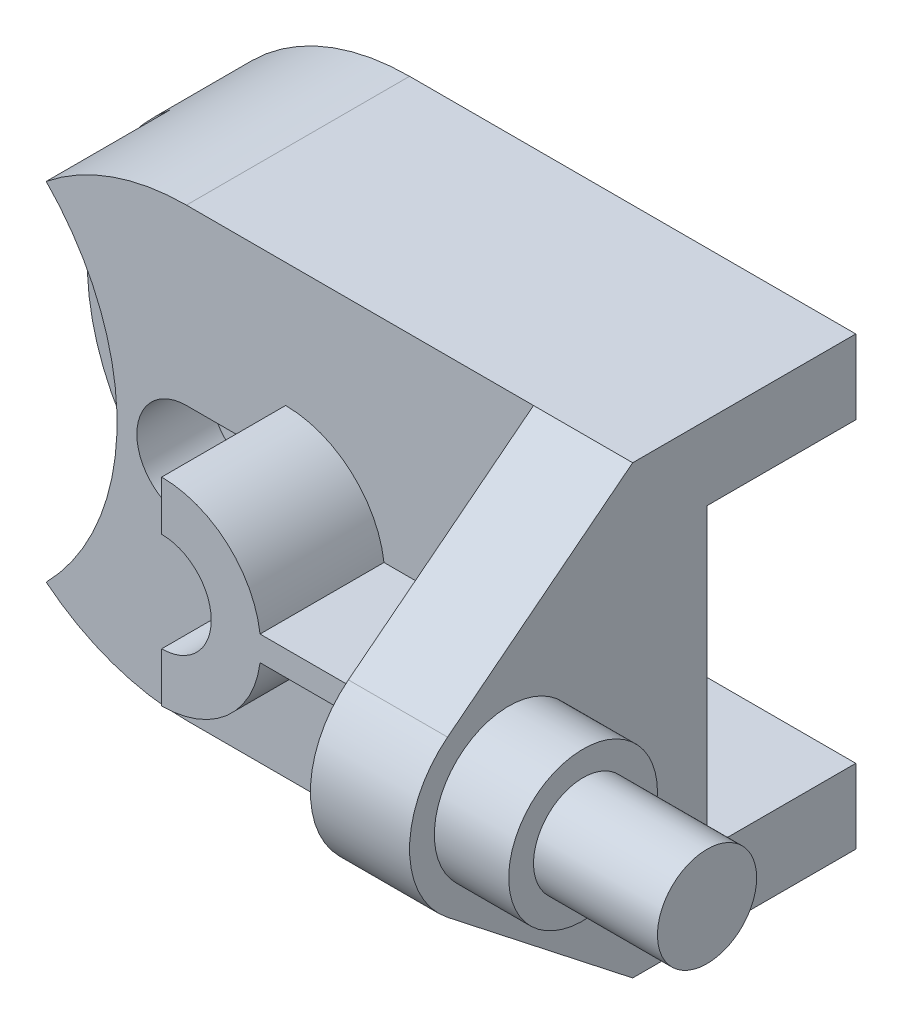
SolidWorks part; units mm, degrees
ref_plane "Front Plane" through (0, 0, 0) normal (0, 0, 1) x (1, 0, 0)
ref_plane "Top Plane" through (0, 0, 0) normal (0, 1, 0) x (1, 0, 0)
ref_plane "Right Plane" through (0, 0, 0) normal (1, 0, 0) x (0, 0, -1)
sketch "Sketch1" plane through (0, 0, 0) normal (0, 0, 1) x (1, 0, 0)
  line L1 (0, 0) -> (175, 0)
  line L2 (0, 0) -> (0, 90)
  line L3 (0, 90) -> (175, 90)
  line L4 (175, 0) -> (175, 90)
  dimension "D1" = 175
  dimension "D2" = 90
extrude "Boss-Extrude1" add sketch "Sketch1" along normal blind 90
sketch "Sketch2" plane through (0, 0, 90) normal (0, 0, 1) x (1, 0, 0)
  line L0 (175, 90) -> (0, 90) construction
  line L1 (0, 90) -> (45, 90)
  line L2 (0, 90) -> (0, 0)
  line L3 (0, 0) -> (45, 0)
  arc A0 (45, 90) -> (45, 0) centre (45, 45) ccw
  line M1 (0, 90) -> (0, 0)
  line M2 (0, 0) -> (175, 0)
  line M4 (175, 90) -> (0, 90)
  dimension "D2" = 45
  dimension "D1" = 45
  dimension "D3" = 45
  dimension "D4" = 45
extrude "Cut-Extrude1" cut sketch "Sketch2" against normal blind 90 contours A0 M4 M1 | A0 L2 M2
sketch "Sketch3" plane through (0, 0, 90) normal (0, 0, 1) x (1, 0, 0)
  line L1 (175, 90) -> (135, 90)
  line L2 (175, 90) -> (175, 60)
  line L3 (175, 60) -> (135, 60)
  line L4 (135, 90) -> (135, 60)
  line L5 (175, 0) -> (135, 0)
  line L6 (175, 0) -> (175, 30)
  line L7 (175, 30) -> (135, 30)
  line L8 (135, 0) -> (135, 30)
  dimension "D1" = 40
  dimension "D2" = 40
  dimension "D3" = 30
  dimension "D4" = 30
extrude "Cut-Extrude2" cut sketch "Sketch3" against normal blind 90
sketch "Sketch4" plane through (0, 0, 90) normal (0, 0, 1) x (1, 0, 0)
  line L1 (175, 60) -> (150, 60)
  line L2 (175, 60) -> (175, 55)
  line L3 (175, 55) -> (150, 55)
  line L4 (150, 60) -> (150, 55)
  line L5 (175, 30) -> (150, 30)
  line L6 (175, 30) -> (175, 35)
  line L7 (175, 35) -> (150, 35)
  line L8 (150, 30) -> (150, 35)
  dimension "D1" = 5
  dimension "D2" = 5
  dimension "D3" = 25
  dimension "D4" = 25
extrude "Cut-Extrude3" cut sketch "Sketch4" against normal blind 90
sketch "Sketch5" plane through (0, 0, 90) normal (0, 0, 1) x (1, 0, 0)
  arc A0 (16.7157, 80) -> (16.7157, 10) centre (-18.9914, 45) cw
  arc A1 (45, 90) -> (45, 0) centre (45, 45) ccw construction
  arc A2 (16.7157, 80) -> (16.7157, 10) centre (45, 45) ccw
  arc M10 (45, 90) -> (45, 0) centre (45, 45) ccw
  dimension "D3" = 50
  dimension "D1" = 10
  dimension "D2" = 10
extrude "Cut-Extrude4" cut sketch "Sketch5" against normal blind 70 contours A0 M10
sketch "Sketch6" plane through (0, 0, 0) normal (1, 0, 0) x (0, 0, -1)
  line L0 (-45, 90) -> (-82.3361, 60.7423)
  line L1 (0, 90) -> (-90, 90) construction
  line L2 (-82.3361, 29.2577) -> (-45, 0)
  line L4 (0, 0) -> (-90, 0) construction
  line L5 (-45, 90) -> (-90, 90)
  line L6 (-90, 90) -> (-90, 0)
  line L7 (-90, 0) -> (-45, 0)
  circle A0 centre (-70, 45) radius 20
  dimension "D1" = 40
  dimension "D2" = 45
  dimension "D3" = 70
  dimension "D4" = 45
  dimension "D5" = 45
extrude "Cut-Extrude5" cut sketch "Sketch6" along normal blind 308 contours A0 L0 L5 L6 | A0 L6 L7 L2
sketch "Sketch7" plane through (0, 0, 0) normal (0, 0, -1) x (-1, 0, 0)
  line L0 (-135, 75) -> (-45, 75)
  line L1 (-135, 90) -> (-135, 60) construction
  line L2 (-135, 75) -> (-135, 15)
  line L3 (-135, 30) -> (-135, 0) construction
  line L4 (-135, 15) -> (-45, 15)
  arc A0 (-45, 75) -> (-45, 15) centre (-45, 45) cw
  dimension "D6" = 30
  dimension "D1" = 15
  dimension "D2" = 15
  dimension "D3" = 90
  dimension "D4" = 90
  dimension "D5" = 60
  dimension "D8" = 30
extrude "Cut-Extrude6" cut sketch "Sketch7" against normal blind 30
sketch "Sketch8" plane through (175, 0, 0) normal (1, 0, 0) x (0, 0, -1)
  line L0 (-87.3205, 55) -> (0, 55)
  line L1 (0, 55) -> (0, 35)
  line L2 (0, 35) -> (-87.3205, 35)
  circle A0 centre (-70, 45) radius 10
  arc A1 (-87.3205, 55) -> (-87.3205, 35) centre (-70, 45) ccw construction
  arc A2 (-87.3205, 55) -> (-87.3205, 35) centre (-70, 45) ccw
  point P2 (-90, 45)
  arc M1 (-87.3205, 55) -> (-87.3205, 35) centre (-70, 45) ccw
  line M2 (-87.3205, 35) -> (0, 35)
  line M3 (0, 35) -> (0, 55)
  line M4 (0, 55) -> (-87.3205, 55)
  dimension "D1" = 20
  dimension "D2" = 20
  dimension "D3" = 45
extrude "Cut-Extrude7" cut sketch "Sketch8" against normal blind 25 contours A0 L0 M1 M2 | A0 L2 M3 M4
sketch "Sketch9" plane through (150, 0, 0) normal (1, 0, 0) x (0, 0, -1)
  line L0 (-83.2288, 60) -> (0, 60)
  line L1 (0, 60) -> (0, 30)
  line L2 (0, 30) -> (-83.2288, 30)
  circle A0 centre (-70, 45) radius 15
  arc A1 (-83.2288, 60) -> (-83.2288, 30) centre (-70, 45) ccw
  line M2 (0, 60) -> (-83.2288, 60)
  arc M3 (-83.2288, 60) -> (-83.2288, 30) centre (-70, 45) ccw
  line M4 (-83.2288, 30) -> (0, 30)
  line M5 (0, 30) -> (0, 60)
  dimension "D1" = 30
extrude "Cut-Extrude8" cut sketch "Sketch9" against normal blind 15 contours A0 L0 M3 M4 | A0 L2 M5 M2
ref_plane "Plane1" through (115, 0, 0) normal (1, 0, 0) x (0, 0, -1)
sketch "Sketch10" plane through (115, 0, 0) normal (1, 0, 0) x (0, 0, -1)
  line L1 (-45, 90) -> (-90, 90)
  line L2 (-45, 90) -> (-45, 0)
  line L3 (-45, 0) -> (-90, 0)
  line L4 (-90, 90) -> (-90, 0)
  dimension "D1" = 45
  dimension "D2" = 45
  dimension "D3" = 0
  dimension "D4" = 0
extrude "Cut-Extrude9" cut sketch "Sketch10" against normal blind 154
sketch "Sketch11" plane through (0, 0, 45) normal (0, 0, 1) x (1, 0, 0)
  line L0 (45, 90) -> (115, 90) construction
  line L1 (65, 55) -> (65, 65)
  line L2 (65, 35) -> (65, 25)
  arc A0 (65, 55) -> (65, 35) centre (65, 45) cw
  arc A1 (65, 65) -> (65, 25) centre (65, 45) cw
  arc A2 (45, 90) -> (45, 0) centre (45, 45) ccw construction
  point P7 (0, 45)
  dimension "D2" = 10
  dimension "D7" = 20
  dimension "D1" = 20
  dimension "D3" = 10
  dimension "D4" = 45
  dimension "D5" = 65
  dimension "D6" = 10
extrude "Boss-Extrude2" add sketch "Sketch11" along normal blind 25
sketch "Sketch12" plane through (0, 0, 45) normal (0, 0, 1) x (1, 0, 0)
  line L0 (65, 45) -> (45, 45) construction
  line L1 (65, 35) -> (45, 35)
  line L2 (65, 55) -> (45, 55)
  arc A0 (65, 35) -> (65, 55) centre (65, 45) ccw
  arc A1 (45, 55) -> (45, 35) centre (45, 45) ccw
  point P3 (55, 45)
  dimension "D2" = 10
  dimension "D1" = 20
extrude "Cut-Extrude10" cut sketch "Sketch12" against normal blind 15
sketch "Sketch13" plane through (0, 0, 45) normal (0, 0, 1) x (1, 0, 0)
  line L0 (115, 0) -> (115, 90) construction
  line L1 (84.8431, 47.5) -> (115, 47.5)
  line L2 (84.8431, 47.5) -> (84.8431, 42.5)
  line L3 (84.8431, 42.5) -> (115, 42.5)
  line L4 (115, 47.5) -> (115, 42.5)
  line L5 (115, 0) -> (45, 0) construction
  line L6 (45, 90) -> (115, 90) construction
  arc A0 (65, 25) -> (65, 65) centre (65, 45) ccw construction
  dimension "D1" = 5
  dimension "D2" = 42.5
  dimension "D3" = 42.5
extrude "Boss-Extrude3" add sketch "Sketch13" along normal blind 25
